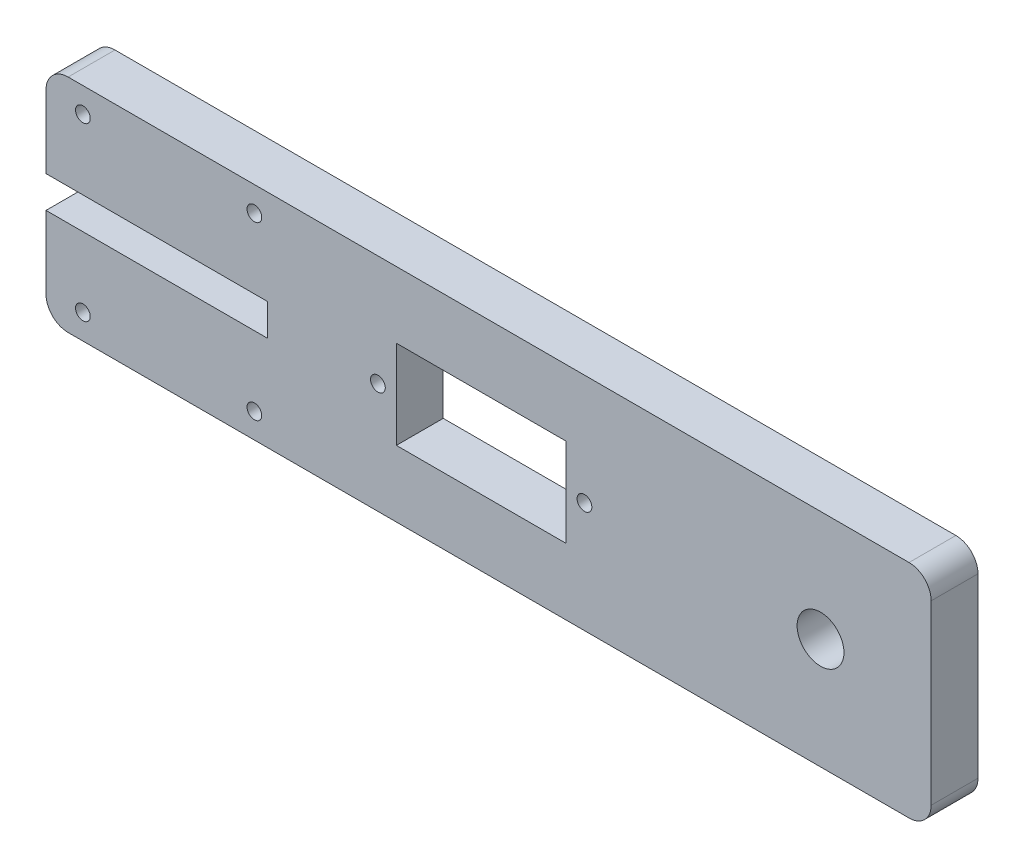
SolidWorks part; units mm, degrees
material "Balsa"
ref_plane "Front Plane" through (0, 0, 0) normal (0, 0, 1) x (1, 0, 0)
ref_plane "Top Plane" through (0, 0, 0) normal (0, 1, 0) x (1, 0, 0)
ref_plane "Right Plane" through (0, 0, 0) normal (1, 0, 0) x (0, 0, -1)
sketch "Sketch1" plane through (0, 0, 0) normal (0, 0, 1) x (1, 0, 0)
  line L0 (0, 17.159) -> (0, 30)
  line L1 (0, 0) -> (120, 0)
  line L2 (0, 0) -> (0, 12.841)
  line L3 (0, 30) -> (120, 30)
  line L4 (120, 0) -> (120, 30)
  line L5 (0, 17.159) -> (30, 17.159)
  line L7 (0, 12.841) -> (30, 12.841)
  line L8 (30, 17.159) -> (30, 12.841)
  dimension "D1" = 30
  dimension "D2" = 120
  dimension "D3" = 4.318
  dimension "D4" = 30
extrude "main shape" add sketch "Sketch1" along normal blind 6.35
fillet "Fillet1" radius 3 4 edges at (0, 0, 3.175) (120, 0, 3.175) (120, 30, 3.175) (0, 30, 3.175)
sketch "elbow X mount hole locations" plane through (0, 0, 6.35) normal (0, 0, 1) x (1, 0, 0)
  line L0 (16.625, 26.625) -> (16.625, 30) construction
  line L1 (5, 26.625) -> (28.25, 26.625) construction
  line L2 (5, 26.625) -> (5, 3.375) construction
  line L3 (5, 3.375) -> (28.25, 3.375) construction
  line L4 (28.25, 26.625) -> (28.25, 3.375) construction
  line L5 (117, 30) -> (3, 30) construction
  line L6 (16.625, 3.375) -> (16.625, 0) construction
  line L7 (3, 0) -> (117, 0) construction
  line L8 (0, 27) -> (0, 17.159) construction
  dimension "D1" = 23.25
  dimension "D2" = 23.25
  dimension "D3" = 5
hole_wizard "elbow X mount holes" positions "Sketch4" profile "Sketch3" tap size "#3-48" standard "Ansi Inch"
sketch "Sketch4" plane through (0, 0, 6.35) normal (0, 0, 1) x (1, 0, 0)
  point P1 (5, 26.625)
  point P4 (28.25, 26.625)
  point P7 (28.25, 3.375)
  point P10 (5, 3.375)
sketch "Sketch3" plane through (5, 26.625, 6.35) normal (1, 0, 0) x (0, -1, 0)
  line L0 (0, 0) -> (0, 8.269)
  line L1 (0, 8.269) -> (0.9969, 7.67)
  line L2 (0.9969, 7.67) -> (0.9969, 0)
  line L5 (0.9969, 0) -> (0, 0)
  line L10 (0, 8.269) -> (-0.997, 7.67) construction
  line L11 (0, -6.35) -> (0, 107.95) construction
  dimension "Tap Drill Dia." = 1.9939
  dimension "Tap Drill Depth" = 7.67
  dimension "Drill Angle" = 118
cosmetic thread "Hole Thread1"
cosmetic thread "Hole Thread2"
cosmetic thread "Hole Thread3"
cosmetic thread "Hole Thread4"
sketch "cutout for elbow support" plane through (0, 0, 0) normal (0, 0, 1) x (1, 0, 0)
  line L1 (0, 0) -> (8.3009, 0)
  line L2 (0, 0) -> (0, 6.7566)
  line L3 (0, 6.7566) -> (8.3009, 6.7566)
  line L4 (8.3009, 0) -> (8.3009, 6.7566)
sketch "Sketch6" plane through (0, 0, 6.35) normal (0, 0, 1) x (1, 0, 0)
  line L0 (0, 15) -> (82.6436, 15) construction
  line L1 (47.5, 21) -> (70.5, 9) construction
  line L2 (47.5, 21) -> (70.5, 21)
  line L3 (47.5, 21) -> (47.5, 9)
  line L4 (47.5, 9) -> (70.5, 9)
  line L5 (70.5, 21) -> (70.5, 9)
  line L6 (70.5, 21) -> (47.5, 9) construction
  line L7 (47.5, 15) -> (45, 15) construction
  line L8 (70.5, 15) -> (73, 15) construction
  line L9 (0, 24.5511) -> (0, 6.7295) construction
  line L10 (0, 27) -> (0, 17.159) construction
  line L11 (0, 12.841) -> (0, 3) construction
  point P3 (45, 15)
  point P4 (73, 15)
  point P11 (59, 15)
  dimension "D1" = 28
  dimension "D2" = 45
  dimension "D3" = 23
  dimension "D4" = 12
extrude "cutout for wrist servo" cut sketch "Sketch6" against normal through all
hole_wizard "wrist servo mounting holes" positions "Sketch8" profile "Sketch7" tap size "#3-48" standard "Ansi Inch" end condition through all
sketch "Sketch8" plane through (0, 0, 6.35) normal (0, 0, 1) x (1, 0, 0)
  point P1 (45, 15)
  point P4 (73, 15)
cosmetic thread "Hole Thread5"
cosmetic thread "Hole Thread6"
sketch "Sketch7" plane through (45, 15, 6.35) normal (1, 0, 0) x (0, -1, 0)
  line L0 (0, 0) -> (0, 6.35)
  line L1 (0, 6.35) -> (0.9969, 6.35)
  line L2 (0.9969, 6.35) -> (0.9969, 0)
  line L5 (0.9969, 0) -> (0, 0)
  line L11 (0, -6.35) -> (0, 107.95) construction
  dimension "Thru Tap Drill Dia." = 1.9939
  dimension "Thru Tap Drill Depth" = 6.35
sketch "wrist dowel hole location" plane through (0, 0, 0) normal (0, 0, 1) x (1, 0, 0)
  line L0 (105, 30) -> (105, 15) construction
  line L1 (117, 30) -> (3, 30) construction
  line L2 (105, 15) -> (105, 0) construction
  line L3 (3, 0) -> (117, 0) construction
  line L4 (120, 3) -> (120, 27) construction
  point P9 (120, 15)
  dimension "D1" = 15
hole_wizard "1/4 (0.25) Diameter Hole (for wrist dowel)" positions "Sketch12" profile "Sketch11" hole size "1/4" standard "Ansi Inch"
sketch "Sketch12" plane through (0, 0, 6.35) normal (0, 0, 1) x (1, 0, 0)
  point P1 (105, 15)
sketch "Sketch11" plane through (105, 15, 6.35) normal (1, 0, 0) x (0, -1, 0)
  line L0 (0, 0) -> (0, 19.9077)
  line L1 (0, 19.9077) -> (3.175, 18)
  line L2 (3.175, 18) -> (3.175, 0)
  line L5 (3.175, 0) -> (0, 0)
  line L10 (0, 19.9077) -> (-3.175, 18) construction
  line L11 (0, -6.35) -> (0, 107.95) construction
  dimension "Hole Dia." = 6.35
  dimension "Hole Depth" = 18
  dimension "Drill Angle" = 118
